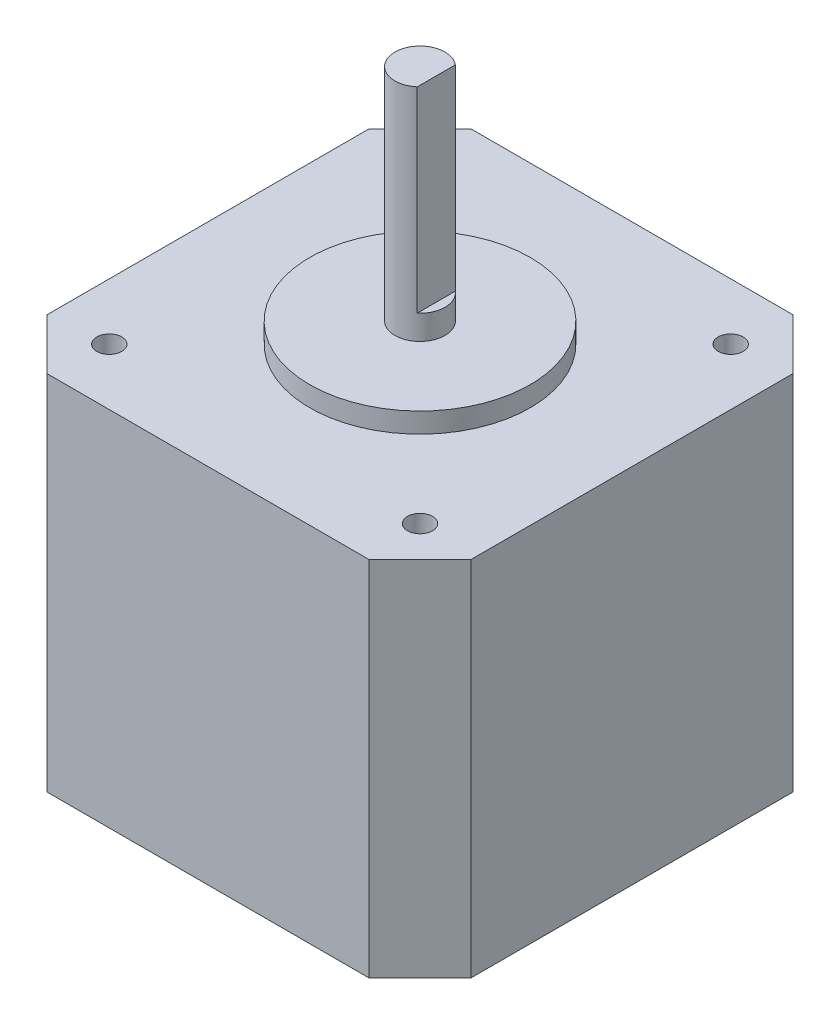
SolidWorks part; units mm, degrees
ref_plane "Front Plane" through (0, 0, 0) normal (0, 0, 1) x (1, 0, 0)
ref_plane "Top Plane" through (0, 0, 0) normal (0, 1, 0) x (1, 0, 0)
ref_plane "Right Plane" through (0, 0, 0) normal (1, 0, 0) x (0, 0, -1)
sketch "Sketch1" plane through (0, 0, 0) normal (0, 1, 0) x (1, 0, 0)
  line L0 (-21.15, 16.07) -> (-16.07, 21.15)
  line L1 (-16.07, 21.15) -> (16.07, 21.15)
  line L2 (-21.15, 16.07) -> (-21.15, -16.07)
  line L3 (-16.07, -21.15) -> (16.07, -21.15)
  line L4 (21.15, 16.07) -> (21.15, -16.07)
  line L5 (-21.15, 21.15) -> (21.15, -21.15) construction
  line L6 (-21.15, -21.15) -> (21.15, 21.15) construction
  line L7 (16.07, 21.15) -> (21.15, 16.07)
  line L8 (16.07, -21.15) -> (21.15, -16.07)
  line L9 (-21.15, -16.07) -> (-16.07, -21.15)
  point P0 (0, 0)
  dimension "D1" = 42.3
  dimension "D2" = 42.3
extrude "Boss-Extrude1" add sketch "Sketch1" along normal blind 36.158
hole_wizard "Tap Drill for M3x0.5 Tap1" positions "Sketch2" profile "Sketch3" hole size "M3x0.5" standard "ANSI Metric"
sketch "Sketch2" plane through (0, 36.158, 0) normal (0, 1, 0) x (1, 0, 0)
  line L1 (0, -1000) -> (0, 49000) construction
  line L2 (-1000, 0) -> (49000, 0) construction
  point P0 (-15.5, 15.5)
  point P2 (15.5, 15.5)
  point P4 (15.5, -15.5)
  point P6 (-15.5, -15.5)
  point P30 (0, 0)
  dimension "D1" = 31
  dimension "D2" = 31
sketch "Sketch3" plane through (-15.5, 36.158, -15.5) normal (1, 0, 0) x (0, 0, 1)
  line L0 (0, 0) -> (0, 13.4511)
  line L1 (0, 13.4511) -> (1.25, 12.7)
  line L2 (1.25, 12.7) -> (1.25, 0)
  line L5 (1.25, 0) -> (0, 0)
  line L10 (0, 13.4511) -> (-1.25, 12.7) construction
  line L11 (0, -6.35) -> (0, 107.95) construction
  dimension "Hole Dia." = 2.5
  dimension "Hole Depth" = 12.7
  dimension "Drill Angle" = 118
sketch "Sketch4" plane through (0, 36.158, 0) normal (0, 1, 0) x (1, 0, 0)
  circle A0 centre (0, 0) radius 11
  dimension "D1" = 22
extrude "Boss-Extrude2" add sketch "Sketch4" along normal blind 2
sketch "Sketch5" plane through (0, 38.158, 0) normal (0, 1, 0) x (1, 0, 0)
  circle A0 centre (0, 0) radius 2.5
  dimension "D1" = 5
extrude "Boss-Extrude3" add sketch "Sketch5" along normal blind 22
sketch "Sketch6" plane through (0, 60.158, 0) normal (0, 1, 0) x (1, 0, 0)
  line L0 (1.6234, 1.9012) -> (1.6234, -1.9012)
  circle A0 centre (0, 0) radius 2.5 construction
  arc A1 (1.6234, -1.9012) -> (1.6234, 1.9012) centre (0, 0) ccw
extrude "Cut-Extrude1" cut sketch "Sketch6" against normal blind 19.558
